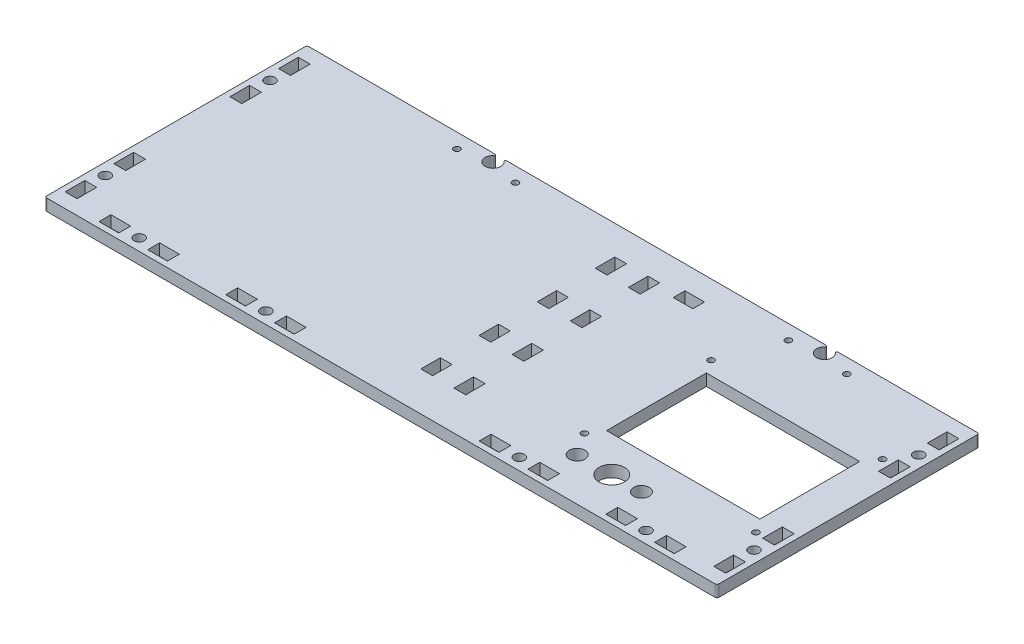
SolidWorks part; units mm, degrees
material "Maple"
ref_plane "Front Plane" through (0, 0, 0) normal (0, 0, 1) x (1, 0, 0)
ref_plane "Top Plane" through (0, 0, 0) normal (0, 1, 0) x (1, 0, 0)
ref_plane "Right Plane" through (0, 0, 0) normal (1, 0, 0) x (0, 0, -1)
sketch "Sketch1" plane through (0, 0, 0) normal (0, 1, 0) x (1, 0, 0)
  line L1 (-172.4, 67.25) -> (172.4, 67.25)
  line L2 (-172.4, 67.25) -> (-172.4, -67.25)
  line L3 (-172.4, -67.25) -> (172.4, -67.25)
  line L4 (172.4, 67.25) -> (172.4, -67.25)
  line L5 (-172.4, 67.25) -> (172.4, -67.25) construction
  line L6 (-172.4, -67.25) -> (172.4, 67.25) construction
  point P0 (0, 0)
  dimension "D1" = 344.8
  dimension "D2" = 134.5
extrude "Boss-Extrude1" add sketch "Sketch1" along normal blind 6
ref_plane "Plane1" through (0, 3, 0) normal (0, -1, 0) x (-1, 0, 0)
sketch "Sketch2" plane through (0, 0, 0) normal (0, -1, 0) x (-1, 0, 0)
  line L0 (-154.05, 24.1) -> (-154.05, -26.9) construction
  line L1 (-154.15, 24.2) -> (-75.5, 24.2)
  line L2 (-154.15, 24.2) -> (-154.15, -27)
  line L3 (-154.15, -27) -> (-75.5, -27)
  line L4 (-75.5, 24.2) -> (-75.5, -27)
  line L5 (-75.6, 24.1) -> (-154.05, 24.1) construction
  line L6 (-75.6, -26.9) -> (-75.6, 24.1) construction
  line L7 (-154.05, -26.9) -> (-75.6, -26.9) construction
  circle A0 centre (-96.4, -45.25) radius 6.5
  circle A1 centre (-96.4, -45.25) radius 6 construction
  circle A2 centre (-78.65, -45.25) radius 4
  circle A4 centre (-111.65, -45.25) radius 4
  circle A5 centre (-111.65, -45.25) radius 1.75 construction
  dimension "D5" = 13
  dimension "D6" = 8
  dimension "D7" = 8
  dimension "D1" = 0.1
  dimension "D2" = 0.1
  dimension "D3" = 0.1
  dimension "D4" = 0.1
extrude "Cut-Extrude1" cut sketch "Sketch2" against normal through all
hole_wizard "M3 Clearance Hole1" positions "Sketch4" profile "Sketch3" hole size "M3" standard "ANSI Metric" end condition through all
sketch "Sketch4" plane through (0, 0, 0) normal (0, -1, 0) x (-1, 0, 0)
  circle A0 centre (-159, 31.1) radius 1.55 construction
  circle A1 centre (-71.05, 31.1) radius 1.55 construction
  circle A2 centre (-71.05, -33.9) radius 1.55 construction
  circle A3 centre (-159, -33.9) radius 1.55 construction
  point P0 (-159, 31.1)
  point P2 (-71.05, 31.1)
  point P4 (-71.05, -33.9)
  point P6 (-159, -33.9)
sketch "Sketch3" plane through (159, 0, -31.1) normal (1, 0, 0) x (0, 0, -1)
  line L0 (0, 0) -> (0, 6)
  line L1 (0, 6) -> (1.6, 6)
  line L2 (1.6, 6) -> (1.6, 0)
  line L5 (1.6, 0) -> (0, 0)
  line L11 (0, -6.35) -> (0, 107.95) construction
  dimension "Thru Hole Dia." = 3.2
  dimension "Thru Hole Depth" = 6
hole_wizard "M5 Clearance Hole1" positions "Sketch6" profile "Sketch5" hole size "M5" standard "ANSI Metric" end condition through all
sketch "Sketch6" plane through (0, 0, 0) normal (0, -1, 0) x (-1, 0, 0)
  line L0 (-172.4, -61.25) -> (172.4, -61.25) construction
  line L1 (-172.4, -67.25) -> (-172.4, 67.25) construction
  line L2 (172.4, 67.25) -> (172.4, -67.25) construction
  line L4 (172.4, -67.25) -> (-172.4, -67.25) construction
  line L5 (0, -61.25) -> (65, -61.25) construction
  line L9 (-166.4, 67.25) -> (-166.4, 42.25) construction
  line L10 (-172.4, 67.25) -> (172.4, 67.25) construction
  line L13 (-166.4, -42.25) -> (-166.4, -67.25) construction
  line L14 (-166.4, 42.25) -> (-166.4, -42.25) construction
  point P0 (0, -61.25)
  point P22 (65, -61.25)
  point P23 (130, -61.25)
  point P33 (-166.4, -42.25)
  point P35 (-166.4, 42.25)
  dimension "D1" = 6
  dimension "D3" = 65
  dimension "D4" = 6
  dimension "D5" = 25
  dimension "D2" = 3
sketch "Sketch5" plane through (0, 0, 61.25) normal (1, 0, 0) x (0, 0, -1)
  line L0 (0, 0) -> (0, 6)
  line L1 (0, 6) -> (2.65, 6)
  line L2 (2.65, 6) -> (2.65, 0)
  line L5 (2.65, 0) -> (0, 0)
  line L11 (0, -6.35) -> (0, 107.95) construction
  dimension "Thru Hole Dia." = 5.3
  dimension "Thru Hole Depth" = 6
mirror "Mirror1" about plane through (0, 0, 0) normal (1, 0, 0) of "M5 Clearance Hole1"
sketch "Sketch7" plane through (122.4, 3, -22.25) normal (0, -1, 0) x (1, 0, 0)
  line L0 (47.05, -37.55) -> (40.95, -37.55)
  line L1 (47, -37.5) -> (41, -37.5) construction
  line L2 (47, -37.5) -> (47, -27.5) construction
  line L3 (47, -27.5) -> (41, -27.5) construction
  line L4 (41, -37.5) -> (41, -27.5) construction
  line L5 (40.95, -37.55) -> (40.95, -27.45)
  line L6 (47.05, -27.45) -> (40.95, -27.45)
  line L7 (47.05, -37.55) -> (47.05, -27.45)
  line L8 (34.1833, -20) -> (-29.1933, -20) construction
  line L9 (41, -12.5) -> (47, -12.5) construction
  line L10 (41, -27.5) -> (47, -27.5) construction
  line L11 (41, -2.5) -> (41, -12.5) construction
  line L12 (47, -12.5) -> (41, -12.5) construction
  line L13 (47, -2.5) -> (47, -12.5) construction
  line L14 (47, -2.5) -> (41, -2.5) construction
  line L15 (47.05, -2.45) -> (47.05, -12.55)
  line L16 (47.05, -12.55) -> (40.95, -12.55)
  line L17 (40.95, -2.45) -> (40.95, -12.55)
  line L18 (47.05, -2.45) -> (40.95, -2.45)
  dimension "D1" = 0.05
extrude "Cut-Extrude2" cut sketch "Sketch7" against normal through all both and the other way through all
other "Smart-Feature1<x_hex cap screw_am-46>"
sketch "Sketch71" plane through (122.4, 3, 62.25) normal (0, -1, 0) x (1, 0, 0)
  line L0 (47.05, -37.55) -> (40.95, -37.55)
  line L1 (47, -37.5) -> (41, -37.5) construction
  line L2 (47, -37.5) -> (47, -27.5) construction
  line L3 (47, -27.5) -> (41, -27.5) construction
  line L4 (41, -37.5) -> (41, -27.5) construction
  line L5 (40.95, -37.55) -> (40.95, -27.45)
  line L6 (47.05, -27.45) -> (40.95, -27.45)
  line L7 (47.05, -37.55) -> (47.05, -27.45)
  line L8 (34.1833, -20) -> (-29.1933, -20) construction
  line L9 (41, -12.5) -> (47, -12.5) construction
  line L10 (41, -27.5) -> (47, -27.5) construction
  line L11 (41, -2.5) -> (41, -12.5) construction
  line L12 (47, -12.5) -> (41, -12.5) construction
  line L13 (47, -2.5) -> (47, -12.5) construction
  line L14 (47, -2.5) -> (41, -2.5) construction
  line L15 (47.05, -2.45) -> (47.05, -12.55)
  line L16 (47.05, -12.55) -> (40.95, -12.55)
  line L17 (40.95, -2.45) -> (40.95, -12.55)
  line L18 (47.05, -2.45) -> (40.95, -2.45)
  dimension "D1" = 0.05
extrude "Cut-Extrude21" cut sketch "Sketch71" against normal through all both and the other way through all
other "Smart-Feature2<x_hex cap screw_am-47>"
sketch "Sketch72" plane through (-210.4, 3, -22.25) normal (0, -1, 0) x (1, 0, 0)
  line L0 (47.05, -37.55) -> (40.95, -37.55)
  line L1 (47, -37.5) -> (41, -37.5) construction
  line L2 (47, -37.5) -> (47, -27.5) construction
  line L3 (47, -27.5) -> (41, -27.5) construction
  line L4 (41, -37.5) -> (41, -27.5) construction
  line L5 (40.95, -37.55) -> (40.95, -27.45)
  line L6 (47.05, -27.45) -> (40.95, -27.45)
  line L7 (47.05, -37.55) -> (47.05, -27.45)
  line L8 (34.1833, -20) -> (-29.1933, -20) construction
  line L9 (41, -12.5) -> (47, -12.5) construction
  line L10 (41, -27.5) -> (47, -27.5) construction
  line L11 (41, -2.5) -> (41, -12.5) construction
  line L12 (47, -12.5) -> (41, -12.5) construction
  line L13 (47, -2.5) -> (47, -12.5) construction
  line L14 (47, -2.5) -> (41, -2.5) construction
  line L15 (47.05, -2.45) -> (47.05, -12.55)
  line L16 (47.05, -12.55) -> (40.95, -12.55)
  line L17 (40.95, -2.45) -> (40.95, -12.55)
  line L18 (47.05, -2.45) -> (40.95, -2.45)
  dimension "D1" = 0.05
extrude "Cut-Extrude22" cut sketch "Sketch72" against normal through all both and the other way through all
other "Smart-Feature3<x_hex cap screw_am-48>"
sketch "Sketch73" plane through (-210.4, 3, 62.25) normal (0, -1, 0) x (1, 0, 0)
  line L0 (47.05, -37.55) -> (40.95, -37.55)
  line L1 (47, -37.5) -> (41, -37.5) construction
  line L2 (47, -37.5) -> (47, -27.5) construction
  line L3 (47, -27.5) -> (41, -27.5) construction
  line L4 (41, -37.5) -> (41, -27.5) construction
  line L5 (40.95, -37.55) -> (40.95, -27.45)
  line L6 (47.05, -27.45) -> (40.95, -27.45)
  line L7 (47.05, -37.55) -> (47.05, -27.45)
  line L8 (34.1833, -20) -> (-29.1933, -20) construction
  line L9 (41, -12.5) -> (47, -12.5) construction
  line L10 (41, -27.5) -> (47, -27.5) construction
  line L11 (41, -2.5) -> (41, -12.5) construction
  line L12 (47, -12.5) -> (41, -12.5) construction
  line L13 (47, -2.5) -> (47, -12.5) construction
  line L14 (47, -2.5) -> (41, -2.5) construction
  line L15 (47.05, -2.45) -> (47.05, -12.55)
  line L16 (47.05, -12.55) -> (40.95, -12.55)
  line L17 (40.95, -2.45) -> (40.95, -12.55)
  line L18 (47.05, -2.45) -> (40.95, -2.45)
  dimension "D1" = 0.05
extrude "Cut-Extrude23" cut sketch "Sketch73" against normal through all both and the other way through all
other "Smart-Feature4<x_hex cap screw_am-49>"
sketch "Sketch74" plane through (150, 3, 105.25) normal (0, -1, 0) x (0, 0, -1)
  line L0 (47.05, -37.55) -> (40.95, -37.55)
  line L1 (47, -37.5) -> (41, -37.5) construction
  line L2 (47, -37.5) -> (47, -27.5) construction
  line L3 (47, -27.5) -> (41, -27.5) construction
  line L4 (41, -37.5) -> (41, -27.5) construction
  line L5 (40.95, -37.55) -> (40.95, -27.45)
  line L6 (47.05, -27.45) -> (40.95, -27.45)
  line L7 (47.05, -37.55) -> (47.05, -27.45)
  line L8 (34.1833, -20) -> (-29.1933, -20) construction
  line L9 (41, -12.5) -> (47, -12.5) construction
  line L10 (41, -27.5) -> (47, -27.5) construction
  line L11 (41, -2.5) -> (41, -12.5) construction
  line L12 (47, -12.5) -> (41, -12.5) construction
  line L13 (47, -2.5) -> (47, -12.5) construction
  line L14 (47, -2.5) -> (41, -2.5) construction
  line L15 (47.05, -2.45) -> (47.05, -12.55)
  line L16 (47.05, -12.55) -> (40.95, -12.55)
  line L17 (40.95, -2.45) -> (40.95, -12.55)
  line L18 (47.05, -2.45) -> (40.95, -2.45)
  dimension "D1" = 0.05
extrude "Cut-Extrude24" cut sketch "Sketch74" against normal through all both and the other way through all
other "Smart-Feature5<x_hex cap screw_am-50>"
sketch "Sketch75" plane through (45, 3, 17.25) normal (0, -1, 0) x (0, 0, 1)
  line L0 (47.05, -37.55) -> (40.95, -37.55)
  line L1 (47, -37.5) -> (41, -37.5) construction
  line L2 (47, -37.5) -> (47, -27.5) construction
  line L3 (47, -27.5) -> (41, -27.5) construction
  line L4 (41, -37.5) -> (41, -27.5) construction
  line L5 (40.95, -37.55) -> (40.95, -27.45)
  line L6 (47.05, -27.45) -> (40.95, -27.45)
  line L7 (47.05, -37.55) -> (47.05, -27.45)
  line L8 (34.1833, -20) -> (-29.1933, -20) construction
  line L9 (41, -12.5) -> (47, -12.5) construction
  line L10 (41, -27.5) -> (47, -27.5) construction
  line L11 (41, -2.5) -> (41, -12.5) construction
  line L12 (47, -12.5) -> (41, -12.5) construction
  line L13 (47, -2.5) -> (47, -12.5) construction
  line L14 (47, -2.5) -> (41, -2.5) construction
  line L15 (47.05, -2.45) -> (47.05, -12.55)
  line L16 (47.05, -12.55) -> (40.95, -12.55)
  line L17 (40.95, -2.45) -> (40.95, -12.55)
  line L18 (47.05, -2.45) -> (40.95, -2.45)
  dimension "D1" = 0.05
extrude "Cut-Extrude25" cut sketch "Sketch75" against normal through all both and the other way through all
other "Smart-Feature6<x_hex cap screw_am-51>"
sketch "Sketch77" plane through (-85, 3, 17.25) normal (0, -1, 0) x (0, 0, 1)
  line L0 (47.05, -37.55) -> (40.95, -37.55)
  line L1 (47, -37.5) -> (41, -37.5) construction
  line L2 (47, -37.5) -> (47, -27.5) construction
  line L3 (47, -27.5) -> (41, -27.5) construction
  line L4 (41, -37.5) -> (41, -27.5) construction
  line L5 (40.95, -37.55) -> (40.95, -27.45)
  line L6 (47.05, -27.45) -> (40.95, -27.45)
  line L7 (47.05, -37.55) -> (47.05, -27.45)
  line L8 (34.1833, -20) -> (-29.1933, -20) construction
  line L9 (41, -12.5) -> (47, -12.5) construction
  line L10 (41, -27.5) -> (47, -27.5) construction
  line L11 (41, -2.5) -> (41, -12.5) construction
  line L12 (47, -12.5) -> (41, -12.5) construction
  line L13 (47, -2.5) -> (47, -12.5) construction
  line L14 (47, -2.5) -> (41, -2.5) construction
  line L15 (47.05, -2.45) -> (47.05, -12.55)
  line L16 (47.05, -12.55) -> (40.95, -12.55)
  line L17 (40.95, -2.45) -> (40.95, -12.55)
  line L18 (47.05, -2.45) -> (40.95, -2.45)
  dimension "D1" = 0.05
extrude "Cut-Extrude27" cut sketch "Sketch77" against normal through all both and the other way through all
other "Smart-Feature8<x_hex cap screw_am-53>"
sketch "Sketch78" plane through (-150, 3, 17.25) normal (0, -1, 0) x (0, 0, 1)
  line L0 (47.05, -37.55) -> (40.95, -37.55)
  line L1 (47, -37.5) -> (41, -37.5) construction
  line L2 (47, -37.5) -> (47, -27.5) construction
  line L3 (47, -27.5) -> (41, -27.5) construction
  line L4 (41, -37.5) -> (41, -27.5) construction
  line L5 (40.95, -37.55) -> (40.95, -27.45)
  line L6 (47.05, -27.45) -> (40.95, -27.45)
  line L7 (47.05, -37.55) -> (47.05, -27.45)
  line L8 (34.1833, -20) -> (-29.1933, -20) construction
  line L9 (41, -12.5) -> (47, -12.5) construction
  line L10 (41, -27.5) -> (47, -27.5) construction
  line L11 (41, -2.5) -> (41, -12.5) construction
  line L12 (47, -12.5) -> (41, -12.5) construction
  line L13 (47, -2.5) -> (47, -12.5) construction
  line L14 (47, -2.5) -> (41, -2.5) construction
  line L15 (47.05, -2.45) -> (47.05, -12.55)
  line L16 (47.05, -12.55) -> (40.95, -12.55)
  line L17 (40.95, -2.45) -> (40.95, -12.55)
  line L18 (47.05, -2.45) -> (40.95, -2.45)
  dimension "D1" = 0.05
extrude "Cut-Extrude28" cut sketch "Sketch78" against normal through all both and the other way through all
other "Smart-Feature9<x_hex cap screw_am-54>"
sketch "Sketch79" plane through (0, 0, 0) normal (0, -1, 0) x (-1, 0, 0)
  line L0 (-100.0237, 67.25) -> (-93.9763, 67.25)
  line L1 (-172.4, 67.25) -> (172.4, 67.25) construction
  line L4 (-99.6458, 66.25) -> (-94.3542, 66.25) construction
  arc A0 (-99.6458, 66.25) -> (-94.3542, 66.25) centre (-97, 63.25) ccw
  circle A1 centre (-97, 63.25) radius 4 construction
  arc A4 (-99.6458, 66.25) -> (-100.0237, 67.25) centre (-100.0237, 66.6786) ccw
  arc A5 (-94.3542, 66.25) -> (-93.9763, 67.25) centre (-93.9763, 66.6786) cw
  dimension "D1" = 1
extrude "Cut-Extrude29" cut sketch "Sketch79" against normal through all
ref_plane "Plane3" through (12, 0, 0) normal (-1, 0, 0) x (0, 0, 1)
mirror "Mirror3" about plane through (12, 0, 0) normal (-1, 0, 0) of "Cut-Extrude29"
sketch "Sketch80" plane through (0, 0, 0) normal (0, -1, 0) x (1, 0, 0)
  line L0 (3.5, -67.25) -> (3.5, 67.25) construction
  line L2 (-172.4, 67.25) -> (172.4, 67.25) construction
  line L3 (3.5, 26.35) -> (3.5, 90.15) construction
  line L4 (3.5, -47.25) -> (3.5, -17.4167) construction
  line L5 (20.5, -67.25) -> (20.5, 67.25) construction
  line L6 (20.5, 26.35) -> (20.5, 90.15) construction
  line L7 (12, -67.25) -> (12, 67.25) construction
  line L8 (93.9763, -67.25) -> (-69.9763, -67.25) construction
  point P8 (3.5, -47.25)
  point P9 (3.5, 42.25)
  point P10 (3.5, -17.4167)
  point P11 (3.5, 12.4167)
  dimension "D2" = 20
  dimension "D3" = 25
  dimension "D1" = 4
sketch "Sketch62" plane through (-40.5, 3, 41.4822) normal (0, -1, 0) x (0, 0, 1)
  line L1 (-4.2322, -41) -> (5.7678, -41)
  line L2 (-4.2322, -41) -> (-4.2322, -47)
  line L3 (-4.2322, -47) -> (5.7678, -47)
  line L4 (5.7678, -41) -> (5.7678, -47)
  line L5 (-4.2322, -41) -> (5.7678, -47) construction
  line L6 (-4.2322, -47) -> (5.7678, -41) construction
  point P0 (0.7678, -44)
  dimension "D1" = 10
  dimension "D2" = 6
extrude "Cut-Extrude12" cut sketch "Sketch62" against normal through all and the other way through all
other "Smart-Feature2<virtual_pin-36>"
sketch "Sketch63" plane through (-40.5, 3, 11.6489) normal (0, -1, 0) x (0, 0, 1)
  line L1 (-4.2322, -41) -> (5.7678, -41)
  line L2 (-4.2322, -41) -> (-4.2322, -47)
  line L3 (-4.2322, -47) -> (5.7678, -47)
  line L4 (5.7678, -41) -> (5.7678, -47)
  line L5 (-4.2322, -41) -> (5.7678, -47) construction
  line L6 (-4.2322, -47) -> (5.7678, -41) construction
  point P0 (0.7678, -44)
  dimension "D1" = 10
  dimension "D2" = 6
extrude "Cut-Extrude13" cut sketch "Sketch63" against normal through all and the other way through all
other "Smart-Feature3<virtual_pin-37>"
sketch "Sketch64" plane through (-40.5, 3, -18.1844) normal (0, -1, 0) x (0, 0, 1)
  line L1 (-4.2322, -41) -> (5.7678, -41)
  line L2 (-4.2322, -41) -> (-4.2322, -47)
  line L3 (-4.2322, -47) -> (5.7678, -47)
  line L4 (5.7678, -41) -> (5.7678, -47)
  line L5 (-4.2322, -41) -> (5.7678, -47) construction
  line L6 (-4.2322, -47) -> (5.7678, -41) construction
  point P0 (0.7678, -44)
  dimension "D1" = 10
  dimension "D2" = 6
extrude "Cut-Extrude14" cut sketch "Sketch64" against normal through all and the other way through all
other "Smart-Feature4<virtual_pin-38>"
sketch "Sketch65" plane through (-40.5, 3, -48.0178) normal (0, -1, 0) x (0, 0, 1)
  line L1 (-4.2322, -41) -> (5.7678, -41)
  line L2 (-4.2322, -41) -> (-4.2322, -47)
  line L3 (-4.2322, -47) -> (5.7678, -47)
  line L4 (5.7678, -41) -> (5.7678, -47)
  line L5 (-4.2322, -41) -> (5.7678, -47) construction
  line L6 (-4.2322, -47) -> (5.7678, -41) construction
  point P0 (0.7678, -44)
  dimension "D1" = 10
  dimension "D2" = 6
extrude "Cut-Extrude15" cut sketch "Sketch65" against normal through all and the other way through all
other "Smart-Feature5<virtual_pin-39>"
ref_plane "Plane2" through (12, 0, 0) normal (1, 0, 0) x (0, 0, -1)
mirror "Mirror2" about plane through (12, 0, 0) normal (1, 0, 0) of "Cut-Extrude15", "Cut-Extrude14", "Cut-Extrude13", "Cut-Extrude12"
sketch "Sketch81" plane through (0, 0, 0) normal (0, -1, 0) x (1, 0, 0)
  circle A0 centre (0, 61.25) radius 2.65 construction
  circle A1 centre (0, 61.25) radius 2.65
extrude "Boss-Extrude2" add sketch "Sketch81" against normal through all
sketch "Sketch82" plane through (0, 0, 0) normal (0, -1, 0) x (-1, 0, 0)
  line L0 (-53.5, 52.25) -> (-23.5, 52.25) construction
  line L1 (-53.5, 55.25) -> (-53.5, 49.25) construction
  line L2 (-23.5, 55.25) -> (-23.5, 49.25) construction
  point P6 (-38.5, 52.25)
sketch "Sketch67" plane through (37.7322, 3, -8.25) normal (0, -1, 0) x (1, 0, 0)
  line L1 (-4.2322, -41) -> (5.7678, -41)
  line L2 (-4.2322, -41) -> (-4.2322, -47)
  line L3 (-4.2322, -47) -> (5.7678, -47)
  line L4 (5.7678, -41) -> (5.7678, -47)
  line L5 (-4.2322, -41) -> (5.7678, -47) construction
  line L6 (-4.2322, -47) -> (5.7678, -41) construction
  point P0 (0.7678, -44)
  dimension "D1" = 10
  dimension "D2" = 6
extrude "Cut-Extrude17" cut sketch "Sketch67" against normal through all and the other way through all
other "Smart-Feature2<virtual_pin-47>"
hole_wizard "M3 Clearance Hole2" positions "Sketch84" profile "Sketch83" hole size "M3" standard "ANSI Metric" end condition through all
sketch "Sketch84" plane through (0, 0, 0) normal (0, -1, 0) x (-1, 0, 0)
  circle A0 centre (-112, 59.75) radius 1.6 construction
  circle A1 centre (-82, 59.75) radius 1.6 construction
  circle A2 centre (58, 59.75) radius 1.6 construction
  circle A3 centre (88, 59.75) radius 1.6 construction
  point P0 (-112, 59.75)
  point P2 (-82, 59.75)
  point P4 (58, 59.75)
  point P6 (88, 59.75)
sketch "Sketch83" plane through (112, 0, -59.75) normal (1, 0, 0) x (0, 0, -1)
  line L0 (0, 0) -> (0, 6)
  line L1 (0, 6) -> (1.6, 6)
  line L2 (1.6, 6) -> (1.6, 0)
  line L5 (1.6, 0) -> (0, 0)
  line L11 (0, -6.35) -> (0, 107.95) construction
  dimension "Thru Hole Dia." = 3.2
  dimension "Thru Hole Depth" = 6
fillet "Fillet1" radius 1 4 edges at (-172.4, 3, 67.25) (-172.4, 3, -67.25) (172.4, 3, -67.25) (172.4, 3, 67.25)
